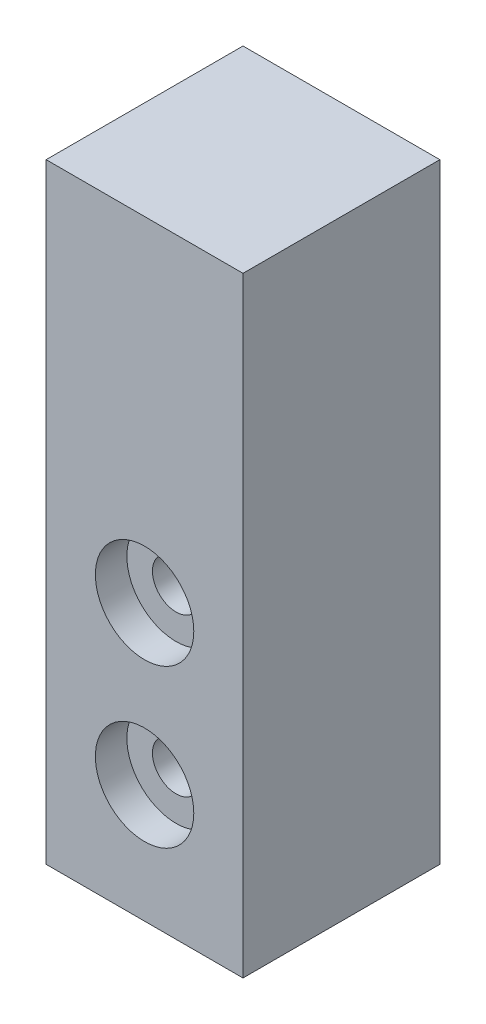
SolidWorks part; units mm, degrees
ref_plane "正面" through (0, 0, 0) normal (0, 0, 1) x (1, 0, 0)
ref_plane "平面" through (0, 0, 0) normal (0, 1, 0) x (1, 0, 0)
ref_plane "右側面" through (0, 0, 0) normal (1, 0, 0) x (0, 0, -1)
sketch "Sketch1" plane through (0, 0, 0) normal (0, 0, 1) x (1, 0, 0)
  line L1 (0, 0) -> (10, 0)
  line L2 (0, 0) -> (0, 31)
  line L3 (0, 31) -> (10, 31)
  line L4 (10, 0) -> (10, 31)
extrude "Boss-Extrude1" add sketch "Sketch1" along normal blind 10
hole_wizard "CBORE for M2 Pan Head Screw1" positions "3DSketch1" profile "Sketch2" counterbore size "M2" standard "JIS"
sketch3d "3DSketch1"
  line L0 (0, 31, 10) -> (0, 0, 10) construction
  line L1 (0, 0, 10) -> (10, 0, 10) construction
  point P0 (5, 14, 10)
  point P2 (5, 6, 10)
  dimension "D1" = 5
  dimension "D2" = 5
  dimension "D3" = 6
  dimension "D4" = 14
sketch "Sketch2" plane through (5, 14, 10) normal (1, 0, 0) x (0, -1, 0)
  line L0 (0, 0) -> (0, 10.721)
  line L1 (0, 10.721) -> (1.2, 10)
  line L2 (1.2, 10) -> (1.2, 1.6)
  line L3 (1.2, 1.6) -> (2.5, 1.6)
  line L4 (2.5, 1.6) -> (2.5, 0)
  line L5 (2.5, 0) -> (0, 0)
  line L10 (0, 10.721) -> (-1.2, 10) construction
  line L11 (0, -6.35) -> (0, 107.95) construction
  dimension "Hole Dia." = 2.4
  dimension "Hole Depth" = 10
  dimension "C'Bore Dia." = 5
  dimension "C'Bore Depth" = 1.6
  dimension "Drill Angle" = 118
